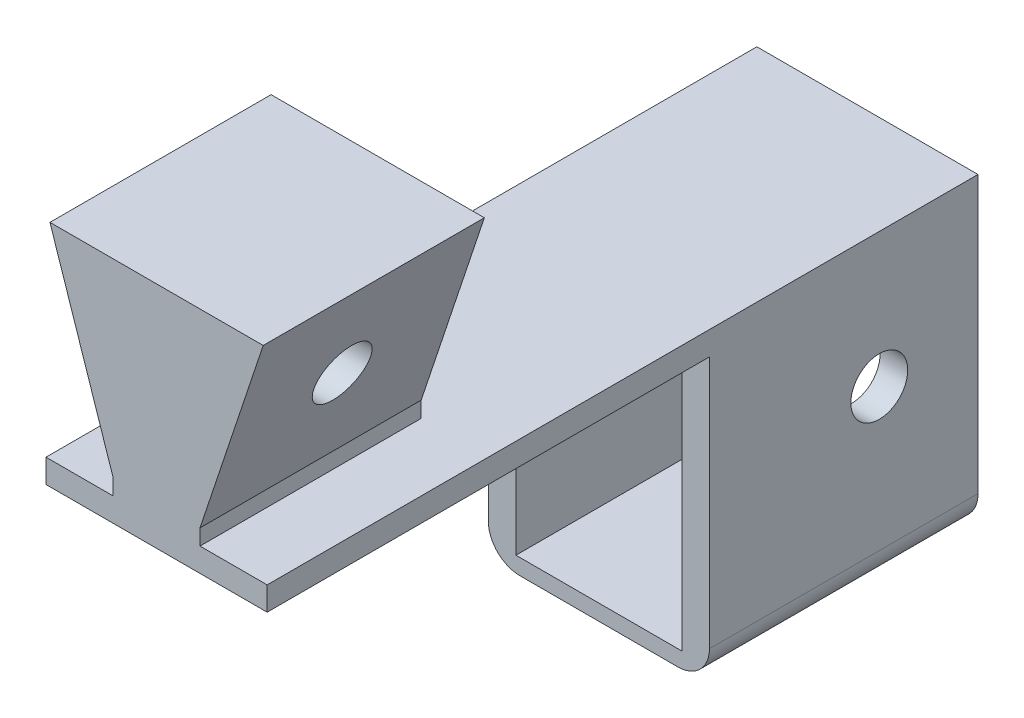
SolidWorks part; units mm, degrees
ref_plane "Front Plane" through (0, 0, 0) normal (0, 0, 1) x (1, 0, 0)
ref_plane "Top Plane" through (0, 0, 0) normal (0, 1, 0) x (1, 0, 0)
ref_plane "Right Plane" through (0, 0, 0) normal (1, 0, 0) x (0, 0, -1)
sketch "Sketch1" plane through (0, 0, 0) normal (0, 0, 1) x (1, 0, 0)
  line L0 (0, 0) -> (5.5, 0)
  line L1 (5.5, 0) -> (5.5, 1)
  line L2 (5.5, 1) -> (9.5, 13)
  line L3 (9.5, 13) -> (-4, 13)
  line L4 (-4, 13) -> (0, 1)
  line L5 (0, 1) -> (0, 0)
  dimension "D1" = 13.5
  dimension "D2" = 5.5
  dimension "D3" = 4
  dimension "D4" = 13
  dimension "D5" = 12
  dimension "D6" = 12
extrude "Boss-Extrude1" add sketch "Sketch1" along normal blind 14
hole_wizard "M3 Clearance Hole1" positions "Sketch2" profile "Sketch3" hole size "M3" standard "ANSI Metric"
sketch "Sketch2" plane through (0, 0, 0) normal (1, 0, 0) x (0, 0, -1)
  line L0 (0, 1) -> (0, 13) construction
  line L1 (-14, 0) -> (0, 0) construction
  point P0 (-7, 7)
  dimension "D1" = 7
  dimension "D2" = 7
sketch "Sketch3" plane through (0, 7, 7) normal (0, 1, 0) x (0, 0, 1)
  line L0 (0, 0) -> (0, 4.25)
  line L1 (0, 4.25) -> (1.8, 4.25)
  line L2 (1.8, 4.25) -> (1.8, 0)
  line L5 (1.8, 0) -> (0, 0)
  line L11 (0, -6.35) -> (0, 107.95) construction
  dimension "Thru Hole Dia." = 3.6
  dimension "Thru Hole Depth" = 4.25
sketch "Sketch4" plane through (0, 0, 0) normal (0, -1, 0) x (1, 0, 0)
  line L0 (-4, 14) -> (0, 14) construction
  line L1 (-4.25, 14) -> (9.75, 14)
  line L2 (-4.25, 14) -> (-4.25, -31)
  line L3 (-4.25, -31) -> (9.75, -31)
  line L4 (9.75, 14) -> (9.75, -31)
  line L5 (0, 14) -> (0, 0) construction
  dimension "D1" = 14
  dimension "D2" = 4.25
  dimension "D3" = 45
extrude "Boss-Extrude2" add sketch "Sketch4" along normal blind 1.5
sketch "Sketch5" plane through (0, -1.5, 0) normal (0, -1, 0) x (1, 0, 0)
  line L0 (9.75, -31) -> (9.75, 14) construction
  line L1 (9.75, -14) -> (8, -14)
  line L2 (9.75, -14) -> (9.75, -31)
  line L3 (9.75, -31) -> (8, -31)
  line L4 (8, -14) -> (8, -31)
  line L5 (-4.25, -31) -> (9.75, -31) construction
  line L6 (-4.25, 14) -> (-4.25, -31) construction
  line L7 (-4.25, -14) -> (-2.5, -14)
  line L8 (-4.25, -14) -> (-4.25, -31)
  line L9 (-4.25, -31) -> (-2.5, -31)
  line L10 (-2.5, -14) -> (-2.5, -31)
  dimension "D1" = 17
  dimension "D2" = 1.75
  dimension "D3" = 1.75
  dimension "D4" = 17
extrude "Boss-Extrude3" add sketch "Sketch5" along normal blind 17
sketch "Sketch6" plane through (0, -18.5, 0) normal (0, -1, 0) x (1, 0, 0)
  line L1 (-4.25, -14) -> (9.75, -14)
  line L2 (-4.25, -14) -> (-4.25, -31)
  line L3 (-4.25, -31) -> (9.75, -31)
  line L4 (9.75, -14) -> (9.75, -31)
extrude "Boss-Extrude4" add sketch "Sketch6" along normal blind 1
hole_wizard "M3 Clearance Hole2" positions "Sketch7" profile "Sketch8" hole size "M3" standard "ANSI Metric"
sketch "Sketch7" plane through (-4.25, 0, 0) normal (-1, 0, 0) x (0, 0, 1)
  line L1 (-14, -19.5) -> (-31, -19.5) construction
  line L2 (0, 13) -> (0, 1) construction
  point P0 (-24.75, -8.5)
  dimension "D1" = 24.75
  dimension "D2" = 11
sketch "Sketch8" plane through (-4.25, -8.5, -24.75) normal (0, 1, 0) x (0, 0, 1)
  line L0 (0, 0) -> (0, 14)
  line L1 (0, 14) -> (1.8, 14)
  line L2 (1.8, 14) -> (1.8, 0)
  line L5 (1.8, 0) -> (0, 0)
  line L11 (0, -6.35) -> (0, 107.95) construction
  dimension "Thru Hole Dia." = 3.6
  dimension "Thru Hole Depth" = 14
fillet "Fillet1" radius 2 2 edges at (9.75, -19.5, -22.5) (-4.25, -19.5, -22.5)
mirror "Mirror1" about plane through (0, 0, 0) normal (1, 0, 0) of "M3 Clearance Hole1"
